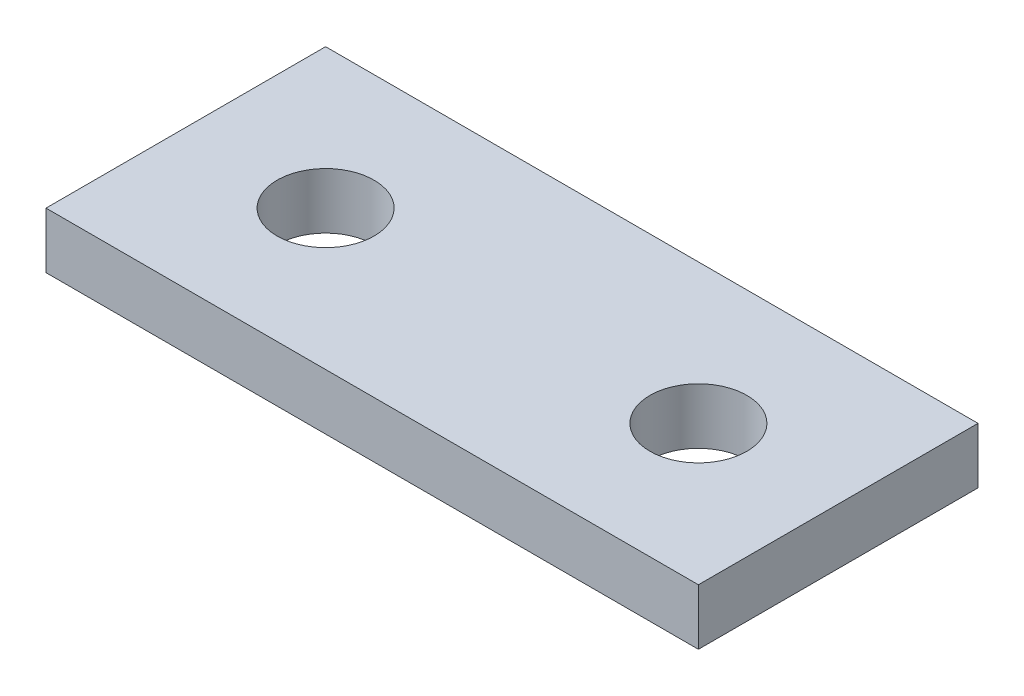
SolidWorks part; units mm, degrees
ref_plane "Спереди" through (0, 0, 0) normal (0, 0, 1) x (1, 0, 0)
ref_plane "Сверху" through (0, 0, 0) normal (0, 1, 0) x (1, 0, 0)
ref_plane "Справа" through (0, 0, 0) normal (1, 0, 0) x (0, 0, -1)
sketch "Эскиз1" plane through (0, 0, 0) normal (0, 1, 0) x (1, 0, 0)
  line L1 (-17.5, 7.5) -> (17.5, 7.5)
  line L2 (-17.5, 7.5) -> (-17.5, -7.5)
  line L3 (-17.5, -7.5) -> (17.5, -7.5)
  line L4 (17.5, 7.5) -> (17.5, -7.5)
  line L5 (-17.5, 7.5) -> (17.5, -7.5) construction
  line L6 (-17.5, -7.5) -> (17.5, 7.5) construction
  circle A1 centre (10, 0) radius 2.6
  circle A2 centre (-10, 0) radius 2.6
  point P0 (0, 0)
extrude "Бобышка-Вытянуть1" add sketch "Эскиз1" along normal blind 3
